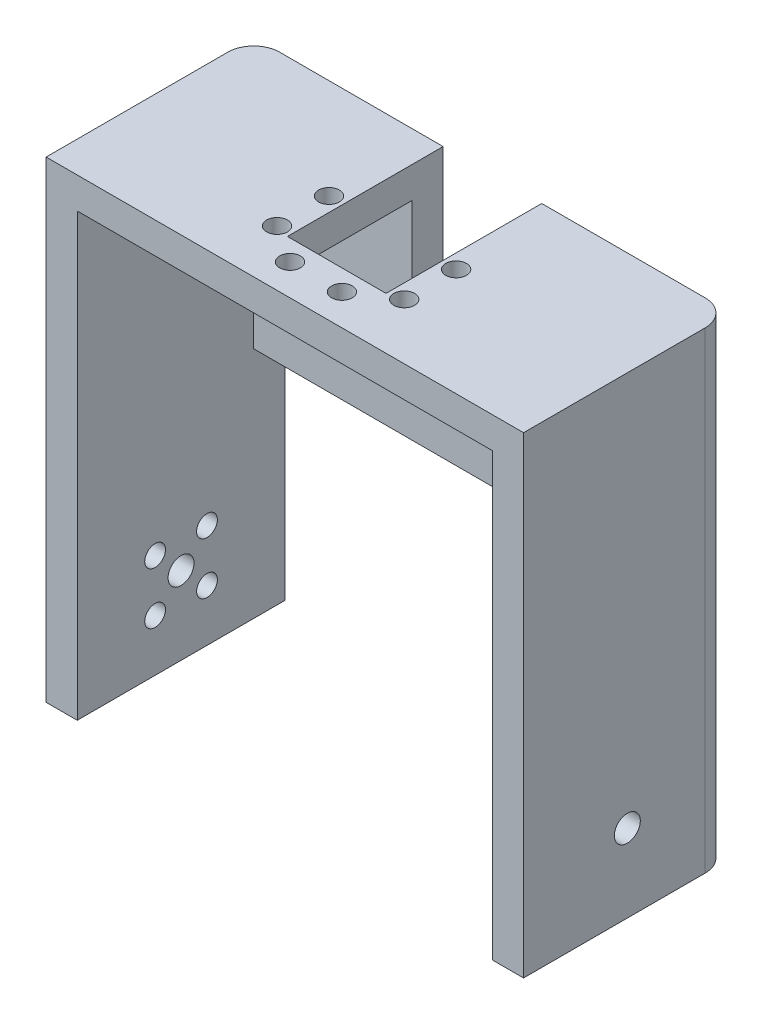
SolidWorks part; units mm, degrees
ref_plane "Alzado" through (0, 0, 0) normal (0, 0, 1) x (1, 0, 0)
ref_plane "Planta" through (0, 0, 0) normal (0, 1, 0) x (1, 0, 0)
ref_plane "Vista lateral" through (0, 0, 0) normal (1, 0, 0) x (0, 0, -1)
sketch "Croquis2" plane through (0, 0, 0) normal (0, 0, 1) x (1, 0, 0)
  line L0 (-40.0265, 0) -> (59.1402, 0) construction
  line L1 (-31.1459, -11.0012) -> (-31.1459, 23.9988)
  line L2 (-31.1459, 23.9988) -> (48.8541, 23.9988)
  line L3 (48.8541, 23.9988) -> (48.8541, -11.0012)
  line L4 (-31.1459, -11.0012) -> (-35.1459, -11.0012)
  line L5 (-35.1459, -11.0012) -> (-35.1459, 27.9988)
  line L6 (48.8541, -11.0012) -> (52.8541, -11.0012)
  line L7 (52.8541, -11.0012) -> (52.8541, 27.9988)
  line L8 (52.8541, 27.9988) -> (-35.1459, 27.9988)
  dimension "D1" = 80
  dimension "D2" = 35
  dimension "D3" = 35
  dimension "D4" = 4
  dimension "D5" = 39
  dimension "D6" = 4
extrude "Saliente-Extruir1" add sketch "Croquis2" along normal blind 40
sketch "Croquis5" plane through (-35.1459, 0, 0) normal (-1, 0, 0) x (0, 0, 1)
  line L0 (0, 27.9988) -> (0, -11.0012) construction
  line L1 (40, -11.0012) -> (0, -11.0012)
  line L2 (40, -11.0012) -> (40, -1.0012)
  line L3 (40, -1.0012) -> (0, -1.0012)
  line L4 (0, -11.0012) -> (0, -1.0012)
  dimension "D1" = 10
extrude "Cortar-Extruir2" cut sketch "Croquis5" against normal blind 40
sketch "Croquis3" plane through (-35.1459, 0, 0) normal (-1, 0, 0) x (0, 0, 1)
  line L0 (40, 27.9988) -> (0, 27.9988) construction
  circle A0 centre (20, 2.9988) radius 2.5
  dimension "D1" = 5
  dimension "D2" = 25
sketch "Croquis7" plane through (0, 0, 40) normal (0, 0, 1) x (1, 0, 0)
  line L0 (-35.1459, -1.0012) -> (-37.1459, -1.0012)
  line L1 (-37.1459, -1.0012) -> (-37.1459, 29.9988)
  line L2 (52.8541, 27.9988) -> (-35.1459, 27.9988) construction
  line L3 (-37.1459, 29.9988) -> (54.8541, 29.9988)
  line L4 (52.8541, -11.0012) -> (52.8541, 27.9988) construction
  line L5 (54.8541, 29.9988) -> (54.8541, -11.0012)
  line L6 (54.8541, -11.0012) -> (52.8541, -11.0012)
  line L7 (52.8541, -11.0012) -> (52.8541, 27.9988)
  line L8 (52.8541, 27.9988) -> (-35.1459, 27.9988)
  line L9 (-35.1459, 27.9988) -> (-35.1459, -1.0012)
  dimension "D1" = 2
  dimension "D2" = 2
  dimension "D3" = 2
extrude "Saliente-Extruir2" add sketch "Croquis7" against normal blind 40
sketch "Croquis6" plane through (0, 27.9988, 0) normal (0, 1, 0) x (1, 0, 0)
  line L0 (54.8541, -40) -> (-37.1459, -40) construction
  line L1 (57.8541, -40) -> (57.8541, 0) construction
  line L3 (11.3541, -35) -> (11.3541, -19) construction
  line L24 (57.8541, -40) -> (57.8541, -20) construction
  line L31 (-0.6459, 12) -> (18.3541, 12)
  line L32 (-0.6459, 12) -> (-0.6459, -30)
  line L33 (-0.6459, -30) -> (18.3541, -30)
  line L34 (18.3541, 12) -> (18.3541, -30)
  circle A8 centre (13.8541, -34) radius 2
  circle A9 centre (3.8541, -34) radius 2
  circle A10 centre (-3.3959, -29.25) radius 2
  circle A11 centre (-3.3959, -19.25) radius 2
  circle A12 centre (21.1041, -19.25) radius 2
  circle A13 centre (21.1041, -29.25) radius 2
  point P51 (11.3541, -30)
  dimension "D8" = 10.75
  dimension "D9" = 4
  dimension "D10" = 4
  dimension "D13" = 36.5
  dimension "D14" = 36.5
  dimension "D15" = 33.75
  dimension "D16" = 41
  dimension "D17" = 10
  dimension "D2" = 10
  dimension "D3" = 16
  dimension "D4" = 6
  dimension "D5" = 6
  dimension "D6" = 19
  dimension "D7" = 42
  dimension "D11" = 10
  dimension "D12" = 10.75
  dimension "D18" = 41
  dimension "D19" = 33.75
extrude "Cortar-Extruir3" cut sketch "Croquis6" against normal through all both and the other way through all
sketch "Croquis9" plane through (0, -1.0012, 0) normal (0, -1, 0) x (1, 0, 0)
  line L1 (-37.1459, 40) -> (-31.1459, 40)
  line L2 (-37.1459, 40) -> (-37.1459, 0)
  line L3 (-37.1459, 0) -> (-31.1459, 0)
  line L4 (-31.1459, 40) -> (-31.1459, 0)
extrude "Saliente-Extruir3" add sketch "Croquis9" along normal blind 60
sketch "Croquis10" plane through (0, -11.0012, 0) normal (0, -1, 0) x (1, 0, 0)
  line L1 (48.8541, 40) -> (54.8541, 40)
  line L2 (48.8541, 40) -> (48.8541, 0)
  line L3 (48.8541, 0) -> (54.8541, 0)
  line L4 (54.8541, 40) -> (54.8541, 0)
extrude "Saliente-Extruir4" add sketch "Croquis10" along normal blind 50
sketch "Croquis11" plane through (-37.1459, 0, 0) normal (-1, 0, 0) x (0, 0, 1)
  circle A0 centre (20, -46.0012) radius 2.5
  dimension "D1" = 15
  dimension "D2" = 20
extrude "Cortar-Extruir4" cut sketch "Croquis11" against normal through all both and the other way through all
sketch "Croquis12" plane through (0, 23.9988, 0) normal (0, -1, 0) x (1, 0, 0)
  line L0 (48.8541, 40) -> (48.8541, 0) construction
  line L1 (-31.1459, 0) -> (48.8541, 0)
  line L2 (-31.1459, 0) -> (-31.1459, 6)
  line L3 (-31.1459, 6) -> (48.8541, 6)
  line L4 (48.8541, 0) -> (48.8541, 6)
  dimension "D1" = 6
extrude "Saliente-Extruir5" add sketch "Croquis12" along normal blind 40
sketch "Croquis13" plane through (0, 0, 0) normal (0, 0, -1) x (-1, 0, 0)
  line L1 (-18.3541, 23.9988) -> (0.6459, 23.9988)
  line L2 (-18.3541, 23.9988) -> (-18.3541, 3.5988)
  line L3 (-18.3541, 3.5988) -> (0.6459, 3.5988)
  line L4 (0.6459, 23.9988) -> (0.6459, 3.5988)
  dimension "D1" = 20.4
  dimension "D2" = 19
extrude "Cortar-Extruir5" cut sketch "Croquis13" against normal blind 40
sketch "Croquis14" plane through (-37.1459, 0, 0) normal (-1, 0, 0) x (0, 0, 1)
  circle A0 centre (25, -51.0012) radius 2
  circle A1 centre (25, -41.0012) radius 2
  circle A2 centre (15, -51.0012) radius 2
  circle A3 centre (15, -41.0012) radius 2
  circle A4 centre (20, -46.0012) radius 2.5
  dimension "D3" = 4
  dimension "D4" = 4
  dimension "D5" = 4
  dimension "D6" = 4
  dimension "D1" = 15
  dimension "D2" = 15
  dimension "D7" = 5
  dimension "D8" = 10
  dimension "D9" = 5
extrude "Cortar-Extruir6" cut sketch "Croquis14" against normal blind 40
fillet "Redondeo3" radius 5 2 edges at (54.8541, -15.5012, 0) (-37.1459, -15.5012, 0)
